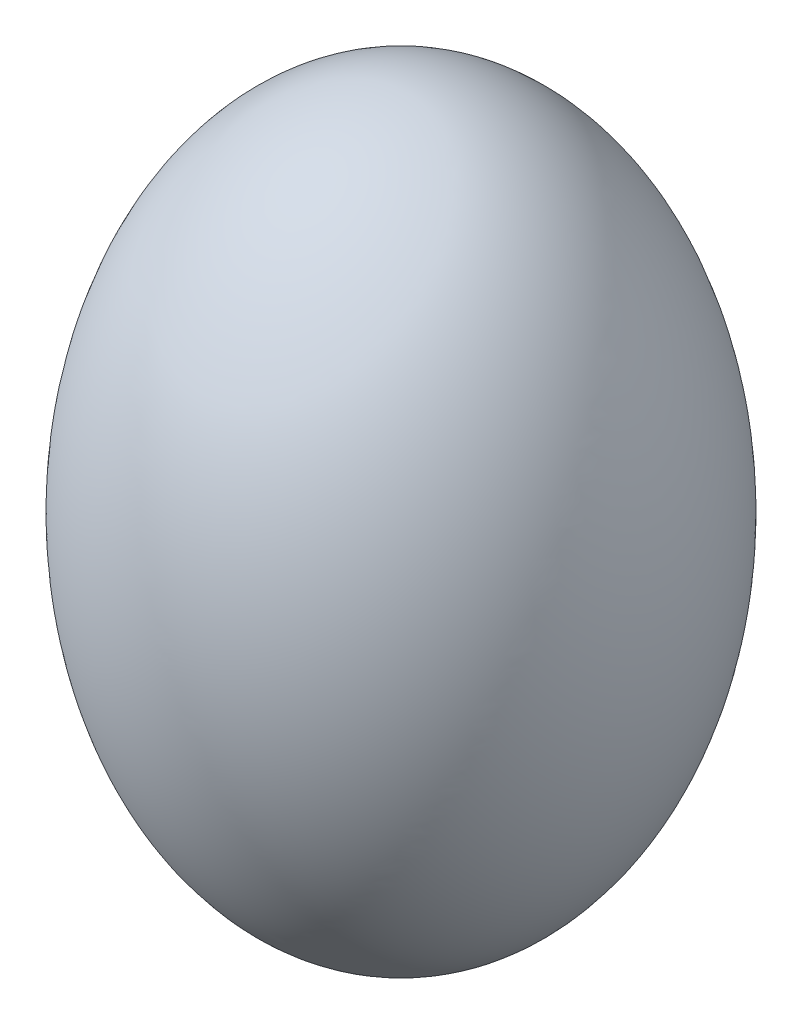
SolidWorks part; units mm, degrees
ref_plane "Ön Düzlem" through (0, 0, 0) normal (0, 0, 1) x (1, 0, 0)
ref_plane "Üst Düzlem" through (0, 0, 0) normal (0, 1, 0) x (1, 0, 0)
ref_plane "Sağ Düzlem" through (0, 0, 0) normal (1, 0, 0) x (0, 0, -1)
sketch "Çizim1" plane through (0, 0, 0) normal (0, 0, 1) x (1, 0, 0)
  line L0 (0, -32.5) -> (0, 32.5)
  ellipse E0 centre (0, 0) end of major axis (0, 32.5) minor radius 22.5 (0, -32.5) -> (0, 32.5) ccw
  dimension "D1" = 65
  dimension "D2" = 22.5
revolve "Döndür1" add sketch "Çizim1" angle 360 about L0
